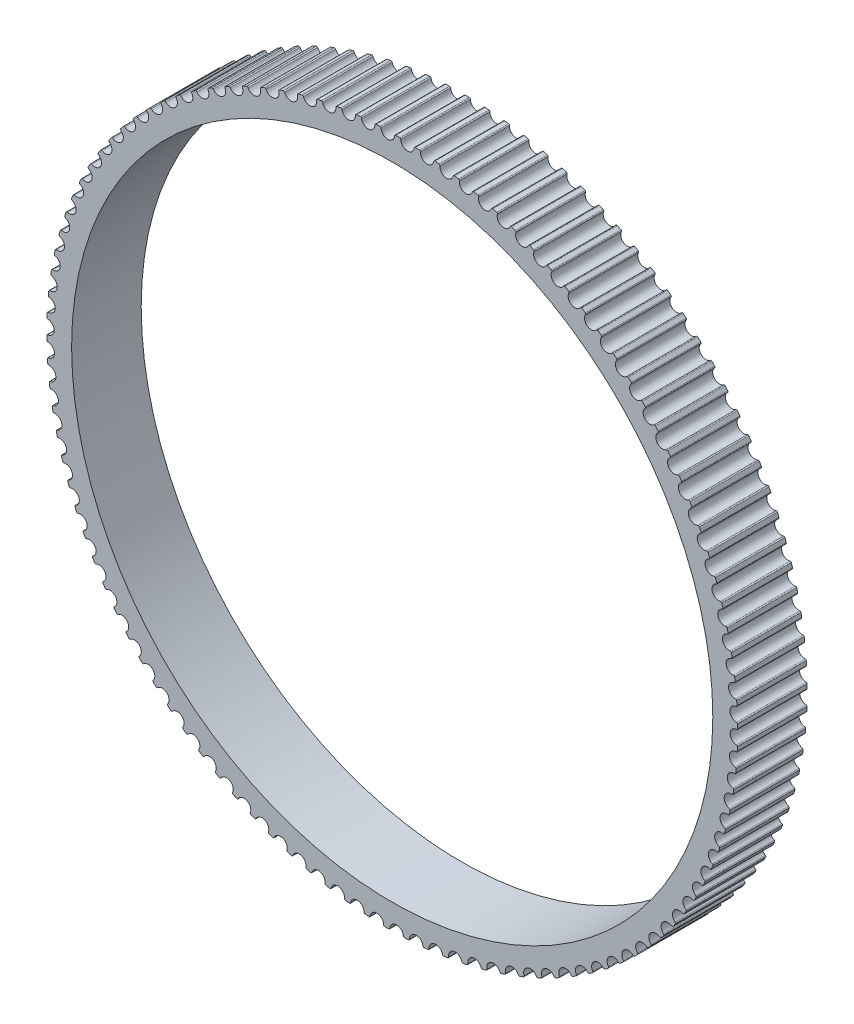
SolidWorks part; units mm, degrees
ref_plane "Front Plane" through (0, 0, 0) normal (0, 0, 1) x (1, 0, 0)
ref_plane "Top Plane" through (0, 0, 0) normal (0, 1, 0) x (1, 0, 0)
ref_plane "Right Plane" through (0, 0, 0) normal (1, 0, 0) x (0, 0, -1)
sketch "Sketch2" plane through (0, 0, 0) normal (0, 0, 1) x (1, 0, 0)
  circle A0 centre (0, 0) radius 35.03 construction
  arc A1 (-3.2113, 34.6013) -> (-3.0921, 34.5062) centre (-3.2012, 34.4918) cw
  arc A2 (-3.0921, 34.5062) -> (-1.738, 34.6009) centre (-2.418, 34.5956) ccw
  arc A3 (-1.738, 34.6009) -> (-1.6332, 34.7116) centre (-1.628, 34.6017) cw
  arc A4 (-1.6332, 34.7116) -> (-1.2307, 34.7282) centre (0, 0) cw
  circle A5 centre (0, 0) radius 34.75 construction
  circle A6 centre (0, 0) radius 34 construction
  arc A7 (0.3511, 34.7482) -> (0.7538, 34.7418) centre (0, 0) cw
  arc A8 (0.2401, 34.6437) -> (0.3511, 34.7482) centre (0.35, 34.6382) cw
  arc A9 (-1.1172, 34.6265) -> (0.2401, 34.6437) centre (-0.4391, 34.6772) ccw
  arc A10 (-1.2307, 34.7282) -> (-1.1172, 34.6265) centre (-1.2269, 34.6183) cw
  arc A11 (2.3343, 34.6715) -> (2.736, 34.6421) centre (0, 0) cw
  arc A12 (2.2175, 34.5735) -> (2.3343, 34.6715) centre (2.3269, 34.5618) cw
  arc A13 (0.8614, 34.6338) -> (2.2175, 34.5735) centre (1.5413, 34.6457) ccw
  arc A14 (0.7538, 34.7418) -> (0.8614, 34.6338) centre (0.7515, 34.6318) cw
  arc A15 (4.3098, 34.4817) -> (4.7092, 34.4294) centre (0, 0) cw
  arc A16 (4.1876, 34.3905) -> (4.3098, 34.4817) centre (4.2962, 34.3726) cw
  arc A17 (2.8372, 34.5281) -> (4.1876, 34.3905) centre (3.5167, 34.5012) ccw
  arc A18 (2.736, 34.6421) -> (2.8372, 34.5281) centre (2.7273, 34.5325) cw
  arc A19 (6.2713, 34.1794) -> (6.6671, 34.1044) centre (0, 0) cw
  arc A20 (6.1441, 34.0953) -> (6.2713, 34.1794) centre (6.2514, 34.0712) cw
  arc A21 (4.8038, 34.3098) -> (6.1441, 34.0953) centre (5.4806, 34.2442) ccw
  arc A22 (4.7092, 34.4294) -> (4.8038, 34.3098) centre (4.6943, 34.3204) cw
  arc A23 (8.2123, 33.7657) -> (8.6032, 33.6682) centre (0, 0) cw
  arc A24 (8.0806, 33.689) -> (8.2123, 33.7657) centre (8.1863, 33.6588) cw
  arc A25 (6.7547, 33.9796) -> (8.0806, 33.689) centre (7.4266, 33.8755) ccw
  arc A26 (6.6671, 34.1044) -> (6.7547, 33.9796) centre (6.646, 33.9965) cw
  arc A27 (10.1266, 33.2418) -> (10.5112, 33.1222) centre (0, 0) cw
  arc A28 (9.9906, 33.1727) -> (10.1266, 33.2418) centre (10.0945, 33.1365) cw
  arc A29 (8.6835, 33.5386) -> (9.9906, 33.1727) centre (9.3484, 33.3962) ccw
  arc A30 (8.6032, 33.6682) -> (8.6835, 33.5386) centre (8.5759, 33.5616) cw
  arc A31 (12.0078, 32.6094) -> (12.385, 32.4681) centre (0, 0) cw
  arc A32 (11.8681, 32.5482) -> (12.0078, 32.6094) centre (11.9698, 32.5062) cw
  arc A33 (10.584, 32.9882) -> (11.8681, 32.5482) centre (11.2397, 32.8081) ccw
  arc A34 (10.5112, 33.1222) -> (10.584, 32.9882) centre (10.4779, 33.0173) cw
  arc A35 (13.8498, 31.8707) -> (14.2183, 31.7081) centre (0, 0) cw
  arc A36 (13.7069, 31.8176) -> (13.8498, 31.8707) centre (13.806, 31.7699) cw
  arc A37 (12.45, 32.3301) -> (13.7069, 31.8176) centre (13.0944, 32.1129) ccw
  arc A38 (12.385, 32.4681) -> (12.45, 32.3301) centre (12.3458, 32.3653) cw
  arc A39 (15.6467, 31.0281) -> (16.0053, 30.8446) centre (0, 0) cw
  arc A40 (15.501, 30.9832) -> (15.6467, 31.0281) centre (15.5972, 30.9299) cw
  arc A41 (14.2754, 31.5667) -> (15.501, 30.9832) centre (14.9063, 31.313) ccw
  arc A42 (14.2183, 31.7081) -> (14.2754, 31.5667) centre (14.1733, 31.6077) cw
  arc A43 (17.3926, 30.0842) -> (17.7401, 29.8806) centre (0, 0) cw
  arc A44 (17.2445, 30.0478) -> (17.3926, 30.0842) centre (17.3375, 29.989) cw
  arc A45 (16.0542, 30.7002) -> (17.2445, 30.0478) centre (16.6696, 30.411) ccw
  arc A46 (16.0053, 30.8446) -> (16.0542, 30.7002) centre (15.9547, 30.747) cw
  arc A47 (19.0817, 29.0423) -> (19.417, 28.8191) centre (0, 0) cw
  arc A48 (18.9318, 29.0143) -> (19.0817, 29.0423) centre (19.0213, 28.9503) cw
  arc A49 (17.7807, 29.7336) -> (18.9318, 29.0143) centre (18.3786, 29.4097) ccw
  arc A50 (17.7401, 29.8806) -> (17.7807, 29.7336) centre (17.684, 29.786) cw
  arc A51 (20.7085, 27.9055) -> (21.0306, 27.6636) centre (0, 0) cw
  arc A52 (20.5573, 27.8862) -> (20.7085, 27.9055) centre (20.643, 27.8172) cw
  arc A53 (19.4491, 28.6701) -> (20.5573, 27.8862) centre (20.0276, 28.3125) ccw
  arc A54 (19.417, 28.8191) -> (19.4491, 28.6701) centre (19.3556, 28.7279) cw
  arc A55 (22.2679, 26.6778) -> (22.5756, 26.4179) centre (0, 0) cw
  arc A56 (22.1158, 26.6671) -> (22.2679, 26.6778) centre (22.1974, 26.5934) cw
  arc A57 (21.0542, 27.513) -> (22.1158, 26.6671) centre (21.6112, 27.123) ccw
  arc A58 (21.0306, 27.6636) -> (21.0542, 27.513) centre (20.964, 27.5761) cw
  arc A59 (23.7545, 25.363) -> (24.0469, 25.086) centre (0, 0) cw
  arc A60 (23.6021, 25.361) -> (23.7545, 25.363) centre (23.6793, 25.2828) cw
  arc A61 (22.5905, 26.2661) -> (23.6021, 25.361) centre (23.1244, 25.845) ccw
  arc A62 (22.5756, 26.4179) -> (22.5905, 26.2661) centre (22.5041, 26.3343) cw
  arc A63 (25.1637, 23.9656) -> (25.4399, 23.6723) centre (0, 0) cw
  arc A64 (25.0114, 23.9723) -> (25.1637, 23.9656) centre (25.0841, 23.8897) cw
  arc A65 (24.0532, 24.9336) -> (25.0114, 23.9723) centre (24.5621, 24.4827) ccw
  arc A66 (24.0469, 25.086) -> (24.0532, 24.9336) centre (23.9708, 25.0066) cw
  arc A67 (26.4909, 22.4899) -> (26.7498, 22.1813) centre (0, 0) cw
  arc A68 (26.3392, 22.5053) -> (26.4909, 22.4899) centre (26.407, 22.4187) cw
  arc A69 (25.4374, 23.5198) -> (26.3392, 22.5053) centre (25.9198, 23.0406) ccw
  arc A70 (25.4399, 23.6723) -> (25.4374, 23.5198) centre (25.3593, 23.5973) cw
  arc A71 (27.7316, 20.9409) -> (27.9725, 20.618) centre (0, 0) cw
  arc A72 (27.581, 20.9649) -> (27.7316, 20.9409) centre (27.6438, 20.8746) cw
  arc A73 (26.7386, 22.0293) -> (27.581, 20.9649) centre (27.1929, 21.5233) ccw
  arc A74 (26.7498, 22.1813) -> (26.7386, 22.0293) centre (26.6651, 22.1111) cw
  arc A75 (28.8819, 19.3236) -> (29.1039, 18.9875) centre (0, 0) cw
  arc A76 (28.7329, 19.3562) -> (28.8819, 19.3236) centre (28.7904, 19.2624) cw
  arc A77 (27.9526, 20.4669) -> (28.7329, 19.3562) centre (28.3772, 19.9358) ccw
  arc A78 (27.9725, 20.618) -> (27.9526, 20.4669) centre (27.8839, 20.5528) cw
  arc A79 (29.9379, 17.6432) -> (30.1404, 17.295) centre (0, 0) cw
  arc A80 (29.7911, 17.6843) -> (29.9379, 17.6432) centre (29.8431, 17.5874) cw
  arc A81 (29.0755, 18.8377) -> (29.7911, 17.6843) centre (29.4691, 18.2832) ccw
  arc A82 (29.1039, 18.9875) -> (29.0755, 18.8377) centre (29.0118, 18.9274) cw
  arc A83 (30.8963, 15.9053) -> (31.0786, 15.5461) centre (0, 0) cw
  arc A84 (30.752, 15.9547) -> (30.8963, 15.9053) centre (30.7985, 15.855) cw
  arc A85 (30.1035, 17.1471) -> (30.752, 15.9547) centre (30.4648, 16.571) ccw
  arc A86 (30.1404, 17.295) -> (30.1035, 17.1471) centre (30.045, 17.2403) cw
  arc A87 (31.7539, 14.1156) -> (31.9154, 13.7465) centre (0, 0) cw
  arc A88 (31.6127, 14.1731) -> (31.7539, 14.1156) centre (31.6534, 14.0709) cw
  arc A89 (31.0333, 15.4006) -> (31.6127, 14.1731) centre (31.3611, 14.8048) ccw
  arc A90 (31.0786, 15.5461) -> (31.0333, 15.4006) centre (30.9802, 15.4969) cw
  arc A91 (32.508, 12.2798) -> (32.6482, 11.9021) centre (0, 0) cw
  arc A92 (32.3703, 12.3452) -> (32.508, 12.2798) centre (32.4051, 12.2409) cw
  arc A93 (31.8619, 13.6038) -> (32.3703, 12.3452) centre (32.1552, 12.9903) ccw
  arc A94 (31.9154, 13.7465) -> (31.8619, 13.6038) centre (31.8144, 13.703) cw
  arc A95 (33.156, 10.4039) -> (33.2744, 10.0189) centre (0, 0) cw
  arc A96 (33.0223, 10.4771) -> (33.156, 10.4039) centre (33.0511, 10.371) cw
  arc A97 (32.5865, 11.7627) -> (33.0223, 10.4771) centre (32.8443, 11.1334) ccw
  arc A98 (32.6482, 11.9021) -> (32.5865, 11.7627) centre (32.5448, 11.8644) cw
  arc A99 (33.6959, 8.4941) -> (33.7921, 8.1029) centre (0, 0) cw
  arc A100 (33.5665, 8.5748) -> (33.6959, 8.4941) centre (33.5892, 8.4672) cw
  arc A101 (33.2049, 9.8831) -> (33.5665, 8.5748) centre (33.4263, 9.2402) ccw
  arc A102 (33.2744, 10.0189) -> (33.2049, 9.8831) centre (33.1691, 9.9871) cw
  arc A103 (34.1259, 6.5566) -> (34.1996, 6.1606) centre (0, 0) cw
  arc A104 (34.0013, 6.6446) -> (34.1259, 6.5566) centre (34.0178, 6.5358) cw
  arc A105 (33.7149, 7.9714) -> (34.0013, 6.6446) centre (33.8993, 7.3169) ccw
  arc A106 (33.7921, 8.1029) -> (33.7149, 7.9714) centre (33.6851, 8.0773) cw
  arc A107 (34.4445, 4.5977) -> (34.4955, 4.1981) centre (0, 0) cw
  arc A108 (34.3252, 4.6926) -> (34.4445, 4.5977) centre (34.3355, 4.5831) cw
  arc A109 (34.115, 6.0337) -> (34.3252, 4.6926) centre (34.2618, 5.3697) ccw
  arc A110 (34.1996, 6.1606) -> (34.115, 6.0337) centre (34.0913, 6.1411) cw
  arc A111 (34.6508, 2.6238) -> (34.6789, 2.2219) centre (0, 0) cw
  arc A112 (34.5371, 2.7254) -> (34.6508, 2.6238) centre (34.5411, 2.6155) cw
  arc A113 (34.4039, 4.0762) -> (34.5371, 2.7254) centre (34.5124, 3.4049) ccw
  arc A114 (34.4955, 4.1981) -> (34.4039, 4.0762) centre (34.3863, 4.1848) cw
  arc A115 (34.7441, 0.6413) -> (34.7492, 0.2385) centre (0, 0) cw
  arc A116 (34.6364, 0.7493) -> (34.7441, 0.6413) centre (34.6341, 0.6393) cw
  arc A117 (34.5805, 2.1055) -> (34.6364, 0.7493) centre (34.6505, 1.4291) ccw
  arc A118 (34.6789, 2.2219) -> (34.5805, 2.1055) centre (34.5691, 2.2149) cw
  arc A119 (34.724, -1.3432) -> (34.7061, -1.7456) centre (0, 0) cw
  arc A120 (34.6227, -1.2293) -> (34.724, -1.3432) centre (34.6141, -1.339) cw
  arc A121 (34.6443, 0.1279) -> (34.6227, -1.2293) centre (34.6756, -0.5514) ccw
  arc A122 (34.7492, 0.2385) -> (34.6443, 0.1279) centre (34.6392, 0.2378) cw
  arc A123 (34.5907, -3.3234) -> (34.5499, -3.7241) centre (0, 0) cw
  arc A124 (34.496, -3.2039) -> (34.5907, -3.3234) centre (34.4812, -3.3129) cw
  arc A125 (34.5951, -1.8501) -> (34.496, -3.2039) centre (34.5876, -2.5301) ccw
  arc A126 (34.7061, -1.7456) -> (34.5951, -1.8501) centre (34.5963, -1.7401) cw
  arc A127 (34.3446, -5.2927) -> (34.2809, -5.6905) centre (0, 0) cw
  arc A128 (34.2569, -5.168) -> (34.3446, -5.2927) centre (34.2359, -5.276) cw
  arc A129 (34.433, -3.8221) -> (34.2569, -5.168) centre (34.3867, -4.5005) ccw
  arc A130 (34.5499, -3.7241) -> (34.433, -3.8221) centre (34.4405, -3.7123) cw
  arc A131 (33.9864, -7.2448) -> (33.9001, -7.6382) centre (0, 0) cw
  arc A132 (33.906, -7.1152) -> (33.9864, -7.2448) centre (33.8788, -7.2218) cw
  arc A133 (34.1587, -5.7816) -> (33.906, -7.1152) centre (34.0737, -6.4563) ccw
  arc A134 (34.2809, -5.6905) -> (34.1587, -5.7816) centre (34.1724, -5.6724) cw
  arc A135 (33.5174, -9.1732) -> (33.4088, -9.5611) centre (0, 0) cw
  arc A136 (33.4445, -9.0393) -> (33.5174, -9.1732) centre (33.4113, -9.1442) cw
  arc A137 (33.7729, -7.7222) -> (33.4445, -9.0393) centre (33.6496, -8.391) ccw
  arc A138 (33.9001, -7.6382) -> (33.7729, -7.7222) centre (33.7928, -7.6141) cw
  arc A139 (32.939, -11.0717) -> (32.8085, -11.4528) centre (0, 0) cw
  arc A140 (32.8739, -10.9338) -> (32.939, -11.0717) centre (32.8348, -11.0367) cw
  arc A141 (33.277, -9.6377) -> (32.8739, -10.9338) centre (33.1157, -10.2983) ccw
  arc A142 (33.4088, -9.5611) -> (33.277, -9.6377) centre (33.303, -9.5308) cw
  arc A143 (32.2532, -12.9341) -> (32.1012, -13.3071) centre (0, 0) cw
  arc A144 (32.1961, -12.7927) -> (32.2532, -12.9341) centre (32.1511, -12.8932) cw
  arc A145 (32.6725, -11.5217) -> (32.1961, -12.7927) centre (32.4737, -12.172) ccw
  arc A146 (32.8085, -11.4528) -> (32.6725, -11.5217) centre (32.7046, -11.4165) cw
  arc A147 (31.4622, -14.7543) -> (31.2891, -15.118) centre (0, 0) cw
  arc A148 (31.4132, -14.6099) -> (31.4622, -14.7543) centre (31.3627, -14.7076) cw
  arc A149 (31.9614, -13.3682) -> (31.4132, -14.6099) centre (31.7259, -14.0061) ccw
  arc A150 (32.1012, -13.3071) -> (31.9614, -13.3682) centre (31.9995, -13.265) cw
  arc A151 (30.5686, -16.5264) -> (30.375, -16.8796) centre (0, 0) cw
  arc A152 (30.5279, -16.3794) -> (30.5686, -16.5264) centre (30.4719, -16.4741) cw
  arc A153 (31.1461, -15.171) -> (30.5279, -16.3794) centre (30.8746, -15.7944) ccw
  arc A154 (31.2891, -15.118) -> (31.1461, -15.171) centre (31.1901, -15.0701) cw
  arc A155 (29.5753, -18.2446) -> (29.3618, -18.5861) centre (0, 0) cw
  arc A156 (29.5431, -18.0955) -> (29.5753, -18.2446) centre (29.4817, -18.1868) cw
  arc A157 (30.2292, -16.9243) -> (29.5431, -18.0955) centre (29.9225, -17.5312) ccw
  arc A158 (30.375, -16.8796) -> (30.2292, -16.9243) centre (30.2789, -16.8262) cw
  arc A159 (28.4855, -19.9032) -> (28.2529, -20.2321) centre (0, 0) cw
  arc A160 (28.4618, -19.7526) -> (28.4855, -19.9032) centre (28.3953, -19.8402) cw
  arc A161 (29.2138, -18.6225) -> (28.4618, -19.7526) centre (28.8729, -19.2109) ccw
  arc A162 (29.3618, -18.5861) -> (29.2138, -18.6225) centre (29.2689, -18.5273) cw
  arc A163 (27.3028, -21.497) -> (27.0518, -21.812) centre (0, 0) cw
  arc A164 (27.2878, -21.3452) -> (27.3028, -21.497) centre (27.2164, -21.4289) cw
  arc A165 (28.103, -20.2599) -> (27.2878, -21.3452) centre (27.7291, -20.8279) ccw
  arc A166 (28.2529, -20.2321) -> (28.103, -20.2599) centre (28.1635, -20.168) cw
  arc A167 (26.031, -23.0206) -> (25.7625, -23.3208) centre (0, 0) cw
  arc A168 (26.0247, -22.8682) -> (26.031, -23.0206) centre (25.9486, -22.9477) cw
  arc A169 (26.9005, -21.8312) -> (26.0247, -22.8682) centre (26.4948, -22.3769) ccw
  arc A170 (27.0518, -21.812) -> (26.9005, -21.8312) centre (26.9662, -21.743) cw
  arc A171 (24.6744, -24.4691) -> (24.3891, -24.7535) centre (0, 0) cw
  arc A172 (24.6767, -24.3167) -> (24.6744, -24.4691) centre (24.5963, -24.3917) cw
  arc A173 (25.6103, -23.3313) -> (24.6767, -24.3167) centre (25.1741, -23.853) ccw
  arc A174 (25.7625, -23.3208) -> (25.6103, -23.3313) centre (25.6809, -23.247) cw
  arc A175 (23.2372, -25.8378) -> (22.9362, -26.1055) centre (0, 0) cw
  arc A176 (23.2483, -25.6858) -> (23.2372, -25.8378) centre (23.1637, -25.7561) cw
  arc A177 (24.2366, -24.7554) -> (23.2483, -25.6858) centre (23.7713, -25.2513) ccw
  arc A178 (24.3891, -24.7535) -> (24.2366, -24.7554) centre (24.3119, -24.6751) cw
  arc A179 (21.7243, -27.1223) -> (21.4084, -27.3723) centre (0, 0) cw
  arc A180 (21.744, -26.9711) -> (21.7243, -27.1223) centre (21.6555, -27.0364) cw
  arc A181 (22.7838, -26.0986) -> (21.744, -26.9711) centre (22.291, -26.5672) ccw
  arc A182 (22.9362, -26.1055) -> (22.7838, -26.0986) centre (22.8636, -26.0228) cw
  arc A183 (20.1405, -28.3183) -> (19.8109, -28.5498) centre (0, 0) cw
  arc A184 (20.1688, -28.1684) -> (20.1405, -28.3183) centre (20.0767, -28.2286) cw
  arc A185 (21.2567, -27.3568) -> (20.1688, -28.1684) centre (20.738, -27.7964) ccw
  arc A186 (21.4084, -27.3723) -> (21.2567, -27.3568) centre (21.3407, -27.2856) cw
  arc A187 (18.491, -29.4219) -> (18.1487, -29.6342) centre (0, 0) cw
  arc A188 (18.5278, -29.2739) -> (18.491, -29.4219) centre (18.4324, -29.3287) cw
  arc A189 (19.6603, -28.5257) -> (18.5278, -29.2739) centre (19.1173, -28.935) ccw
  arc A190 (19.8109, -28.5498) -> (19.6603, -28.5257) centre (19.7481, -28.4595) cw
  arc A191 (16.7811, -30.4295) -> (16.4273, -30.622) centre (0, 0) cw
  arc A192 (16.8263, -30.2839) -> (16.7811, -30.4295) centre (16.728, -30.3332) cw
  arc A193 (17.9997, -29.6015) -> (16.8263, -30.2839) centre (17.4342, -29.9792) ccw
  arc A194 (18.1487, -29.6342) -> (17.9997, -29.6015) centre (18.0912, -29.5404) cw
  arc A195 (15.0166, -31.3379) -> (14.6523, -31.5099) centre (0, 0) cw
  arc A196 (15.07, -31.1951) -> (15.0166, -31.3379) centre (14.969, -31.2387) cw
  arc A197 (16.2805, -30.5808) -> (15.07, -31.1951) centre (15.6943, -30.9256) ccw
  arc A198 (16.4273, -30.622) -> (16.2805, -30.5808) centre (16.3753, -30.5251) cw
  arc A199 (13.203, -32.1441) -> (12.8296, -32.295) centre (0, 0) cw
  arc A200 (13.2646, -32.0046) -> (13.203, -32.1441) centre (13.1613, -32.0423) cw
  arc A201 (14.5081, -31.4604) -> (13.2646, -32.0046) centre (13.9032, -31.7711) ccw
  arc A202 (14.6523, -31.5099) -> (14.5081, -31.4604) centre (14.6059, -31.4101) cw
  arc A203 (11.3464, -32.8454) -> (10.965, -32.9747) centre (0, 0) cw
  arc A204 (11.4158, -32.7096) -> (11.3464, -32.8454) centre (11.3105, -32.7414) cw
  arc A205 (12.6884, -32.2373) -> (11.4158, -32.7096) centre (12.0668, -32.513) ccw
  arc A206 (12.8296, -32.295) -> (12.6884, -32.2373) centre (12.789, -32.1927) cw
  arc A207 (9.4528, -33.4396) -> (9.0646, -33.5469) centre (0, 0) cw
  arc A208 (9.5299, -33.308) -> (9.4528, -33.4396) centre (9.4229, -33.3337) cw
  arc A209 (10.8273, -32.9091) -> (9.5299, -33.308) centre (10.191, -33.1489) ccw
  arc A210 (10.965, -32.9747) -> (10.8273, -32.9091) centre (10.9302, -32.8703) cw
  arc A211 (7.5284, -33.9247) -> (7.1347, -34.0097) centre (0, 0) cw
  arc A212 (7.6128, -33.7977) -> (7.5284, -33.9247) centre (7.5046, -33.8173) cw
  arc A213 (8.9309, -33.4736) -> (7.6128, -33.7977) centre (8.2819, -33.6766) ccw
  arc A214 (9.0646, -33.5469) -> (8.9309, -33.4736) centre (9.0359, -33.4407) cw
  arc A215 (5.5794, -34.2992) -> (5.1814, -34.3615) centre (0, 0) cw
  arc A216 (5.6709, -34.1772) -> (5.5794, -34.2992) centre (5.5617, -34.1906) cw
  arc A217 (7.0054, -33.9288) -> (5.6709, -34.1772) centre (6.3459, -34.0945) ccw
  arc A218 (7.1347, -34.0097) -> (7.0054, -33.9288) centre (7.1121, -33.902) cw
  arc A219 (3.6122, -34.5617) -> (3.2113, -34.6013) centre (0, 0) cw
  arc A220 (3.7105, -34.4452) -> (3.6122, -34.5617) centre (3.6008, -34.4523) cw
  arc A221 (5.057, -34.2734) -> (3.7105, -34.4452) centre (4.3891, -34.4011) ccw
  arc A222 (5.1814, -34.3615) -> (5.057, -34.2734) centre (5.165, -34.2528) cw
  arc A223 (1.6332, -34.7116) -> (1.2307, -34.7282) centre (0, 0) cw
  arc A224 (1.738, -34.6009) -> (1.6332, -34.7116) centre (1.628, -34.6017) cw
  arc A225 (3.0921, -34.5062) -> (1.738, -34.6009) centre (2.418, -34.5956) ccw
  arc A226 (3.2113, -34.6013) -> (3.0921, -34.5062) centre (3.2012, -34.4918) cw
  arc A227 (-0.3511, -34.7482) -> (-0.7538, -34.7418) centre (0, 0) cw
  arc A228 (-0.2401, -34.6437) -> (-0.3511, -34.7482) centre (-0.35, -34.6382) cw
  arc A229 (1.1172, -34.6265) -> (-0.2401, -34.6437) centre (0.4391, -34.6772) ccw
  arc A230 (1.2307, -34.7282) -> (1.1172, -34.6265) centre (1.2269, -34.6183) cw
  arc A231 (-2.3343, -34.6715) -> (-2.736, -34.6421) centre (0, 0) cw
  arc A232 (-2.2175, -34.5735) -> (-2.3343, -34.6715) centre (-2.3269, -34.5618) cw
  arc A233 (-0.8614, -34.6338) -> (-2.2175, -34.5735) centre (-1.5413, -34.6457) ccw
  arc A234 (-0.7538, -34.7418) -> (-0.8614, -34.6338) centre (-0.7515, -34.6318) cw
  arc A235 (-4.3098, -34.4817) -> (-4.7092, -34.4294) centre (0, 0) cw
  arc A236 (-4.1876, -34.3905) -> (-4.3098, -34.4817) centre (-4.2962, -34.3726) cw
  arc A237 (-2.8372, -34.5281) -> (-4.1876, -34.3905) centre (-3.5167, -34.5012) ccw
  arc A238 (-2.736, -34.6421) -> (-2.8372, -34.5281) centre (-2.7273, -34.5325) cw
  arc A239 (-6.2713, -34.1794) -> (-6.6671, -34.1044) centre (0, 0) cw
  arc A240 (-6.1441, -34.0953) -> (-6.2713, -34.1794) centre (-6.2514, -34.0712) cw
  arc A241 (-4.8038, -34.3098) -> (-6.1441, -34.0953) centre (-5.4806, -34.2442) ccw
  arc A242 (-4.7092, -34.4294) -> (-4.8038, -34.3098) centre (-4.6943, -34.3204) cw
  arc A243 (-8.2123, -33.7657) -> (-8.6032, -33.6682) centre (0, 0) cw
  arc A244 (-8.0806, -33.689) -> (-8.2123, -33.7657) centre (-8.1863, -33.6588) cw
  arc A245 (-6.7547, -33.9796) -> (-8.0806, -33.689) centre (-7.4266, -33.8755) ccw
  arc A246 (-6.6671, -34.1044) -> (-6.7547, -33.9796) centre (-6.646, -33.9965) cw
  arc A247 (-10.1266, -33.2418) -> (-10.5112, -33.1222) centre (0, 0) cw
  arc A248 (-9.9906, -33.1727) -> (-10.1266, -33.2418) centre (-10.0945, -33.1365) cw
  arc A249 (-8.6835, -33.5386) -> (-9.9906, -33.1727) centre (-9.3484, -33.3962) ccw
  arc A250 (-8.6032, -33.6682) -> (-8.6835, -33.5386) centre (-8.5759, -33.5616) cw
  arc A251 (-12.0078, -32.6094) -> (-12.385, -32.4681) centre (0, 0) cw
  arc A252 (-11.8681, -32.5482) -> (-12.0078, -32.6094) centre (-11.9698, -32.5062) cw
  arc A253 (-10.584, -32.9882) -> (-11.8681, -32.5482) centre (-11.2397, -32.8081) ccw
  arc A254 (-10.5112, -33.1222) -> (-10.584, -32.9882) centre (-10.4779, -33.0173) cw
  arc A255 (-13.8498, -31.8707) -> (-14.2183, -31.7081) centre (0, 0) cw
  arc A256 (-13.7069, -31.8176) -> (-13.8498, -31.8707) centre (-13.806, -31.7699) cw
  arc A257 (-12.45, -32.3301) -> (-13.7069, -31.8176) centre (-13.0944, -32.1129) ccw
  arc A258 (-12.385, -32.4681) -> (-12.45, -32.3301) centre (-12.3458, -32.3653) cw
  arc A259 (-15.6467, -31.0281) -> (-16.0053, -30.8446) centre (0, 0) cw
  arc A260 (-15.501, -30.9832) -> (-15.6467, -31.0281) centre (-15.5972, -30.9299) cw
  arc A261 (-14.2754, -31.5667) -> (-15.501, -30.9832) centre (-14.9063, -31.313) ccw
  arc A262 (-14.2183, -31.7081) -> (-14.2754, -31.5667) centre (-14.1733, -31.6077) cw
  arc A263 (-17.3926, -30.0842) -> (-17.7401, -29.8806) centre (0, 0) cw
  arc A264 (-17.2445, -30.0478) -> (-17.3926, -30.0842) centre (-17.3375, -29.989) cw
  arc A265 (-16.0542, -30.7002) -> (-17.2445, -30.0478) centre (-16.6696, -30.411) ccw
  arc A266 (-16.0053, -30.8446) -> (-16.0542, -30.7002) centre (-15.9547, -30.747) cw
  arc A267 (-19.0817, -29.0423) -> (-19.417, -28.8191) centre (0, 0) cw
  arc A268 (-18.9318, -29.0143) -> (-19.0817, -29.0423) centre (-19.0213, -28.9503) cw
  arc A269 (-17.7807, -29.7336) -> (-18.9318, -29.0143) centre (-18.3786, -29.4097) ccw
  arc A270 (-17.7401, -29.8806) -> (-17.7807, -29.7336) centre (-17.684, -29.786) cw
  arc A271 (-20.7085, -27.9055) -> (-21.0306, -27.6636) centre (0, 0) cw
  arc A272 (-20.5573, -27.8862) -> (-20.7085, -27.9055) centre (-20.643, -27.8172) cw
  arc A273 (-19.4491, -28.6701) -> (-20.5573, -27.8862) centre (-20.0276, -28.3125) ccw
  arc A274 (-19.417, -28.8191) -> (-19.4491, -28.6701) centre (-19.3556, -28.7279) cw
  arc A275 (-22.2679, -26.6778) -> (-22.5756, -26.4179) centre (0, 0) cw
  arc A276 (-22.1158, -26.6671) -> (-22.2679, -26.6778) centre (-22.1974, -26.5934) cw
  arc A277 (-21.0542, -27.513) -> (-22.1158, -26.6671) centre (-21.6112, -27.123) ccw
  arc A278 (-21.0306, -27.6636) -> (-21.0542, -27.513) centre (-20.964, -27.5761) cw
  arc A279 (-23.7545, -25.363) -> (-24.0469, -25.086) centre (0, 0) cw
  arc A280 (-23.6021, -25.361) -> (-23.7545, -25.363) centre (-23.6793, -25.2828) cw
  arc A281 (-22.5905, -26.2661) -> (-23.6021, -25.361) centre (-23.1244, -25.845) ccw
  arc A282 (-22.5756, -26.4179) -> (-22.5905, -26.2661) centre (-22.5041, -26.3343) cw
  arc A283 (-25.1637, -23.9656) -> (-25.4399, -23.6723) centre (0, 0) cw
  arc A284 (-25.0114, -23.9723) -> (-25.1637, -23.9656) centre (-25.0841, -23.8897) cw
  arc A285 (-24.0532, -24.9336) -> (-25.0114, -23.9723) centre (-24.5621, -24.4827) ccw
  arc A286 (-24.0469, -25.086) -> (-24.0532, -24.9336) centre (-23.9708, -25.0066) cw
  arc A287 (-26.4909, -22.4899) -> (-26.7498, -22.1813) centre (0, 0) cw
  arc A288 (-26.3392, -22.5053) -> (-26.4909, -22.4899) centre (-26.407, -22.4187) cw
  arc A289 (-25.4374, -23.5198) -> (-26.3392, -22.5053) centre (-25.9198, -23.0406) ccw
  arc A290 (-25.4399, -23.6723) -> (-25.4374, -23.5198) centre (-25.3593, -23.5973) cw
  arc A291 (-27.7316, -20.9409) -> (-27.9725, -20.618) centre (0, 0) cw
  arc A292 (-27.581, -20.9649) -> (-27.7316, -20.9409) centre (-27.6438, -20.8746) cw
  arc A293 (-26.7386, -22.0293) -> (-27.581, -20.9649) centre (-27.1929, -21.5233) ccw
  arc A294 (-26.7498, -22.1813) -> (-26.7386, -22.0293) centre (-26.6651, -22.1111) cw
  arc A295 (-28.8819, -19.3236) -> (-29.1039, -18.9875) centre (0, 0) cw
  arc A296 (-28.7329, -19.3562) -> (-28.8819, -19.3236) centre (-28.7904, -19.2624) cw
  arc A297 (-27.9526, -20.4669) -> (-28.7329, -19.3562) centre (-28.3772, -19.9358) ccw
  arc A298 (-27.9725, -20.618) -> (-27.9526, -20.4669) centre (-27.8839, -20.5528) cw
  arc A299 (-29.9379, -17.6432) -> (-30.1404, -17.295) centre (0, 0) cw
  arc A300 (-29.7911, -17.6843) -> (-29.9379, -17.6432) centre (-29.8431, -17.5874) cw
  arc A301 (-29.0755, -18.8377) -> (-29.7911, -17.6843) centre (-29.4691, -18.2832) ccw
  arc A302 (-29.1039, -18.9875) -> (-29.0755, -18.8377) centre (-29.0118, -18.9274) cw
  arc A303 (-30.8963, -15.9053) -> (-31.0786, -15.5461) centre (0, 0) cw
  arc A304 (-30.752, -15.9547) -> (-30.8963, -15.9053) centre (-30.7985, -15.855) cw
  arc A305 (-30.1035, -17.1471) -> (-30.752, -15.9547) centre (-30.4648, -16.571) ccw
  arc A306 (-30.1404, -17.295) -> (-30.1035, -17.1471) centre (-30.045, -17.2403) cw
  arc A307 (-31.7539, -14.1156) -> (-31.9154, -13.7465) centre (0, 0) cw
  arc A308 (-31.6127, -14.1731) -> (-31.7539, -14.1156) centre (-31.6534, -14.0709) cw
  arc A309 (-31.0333, -15.4006) -> (-31.6127, -14.1731) centre (-31.3611, -14.8048) ccw
  arc A310 (-31.0786, -15.5461) -> (-31.0333, -15.4006) centre (-30.9802, -15.4969) cw
  arc A311 (-32.508, -12.2798) -> (-32.6482, -11.9021) centre (0, 0) cw
  arc A312 (-32.3703, -12.3452) -> (-32.508, -12.2798) centre (-32.4051, -12.2409) cw
  arc A313 (-31.8619, -13.6038) -> (-32.3703, -12.3452) centre (-32.1552, -12.9903) ccw
  arc A314 (-31.9154, -13.7465) -> (-31.8619, -13.6038) centre (-31.8144, -13.703) cw
  arc A315 (-33.156, -10.4039) -> (-33.2744, -10.0189) centre (0, 0) cw
  arc A316 (-33.0223, -10.4771) -> (-33.156, -10.4039) centre (-33.0511, -10.371) cw
  arc A317 (-32.5865, -11.7627) -> (-33.0223, -10.4771) centre (-32.8443, -11.1334) ccw
  arc A318 (-32.6482, -11.9021) -> (-32.5865, -11.7627) centre (-32.5448, -11.8644) cw
  arc A319 (-33.6959, -8.4941) -> (-33.7921, -8.1029) centre (0, 0) cw
  arc A320 (-33.5665, -8.5748) -> (-33.6959, -8.4941) centre (-33.5892, -8.4672) cw
  arc A321 (-33.2049, -9.8831) -> (-33.5665, -8.5748) centre (-33.4263, -9.2402) ccw
  arc A322 (-33.2744, -10.0189) -> (-33.2049, -9.8831) centre (-33.1691, -9.9871) cw
  arc A323 (-34.1259, -6.5566) -> (-34.1996, -6.1606) centre (0, 0) cw
  arc A324 (-34.0013, -6.6446) -> (-34.1259, -6.5566) centre (-34.0178, -6.5358) cw
  arc A325 (-33.7149, -7.9714) -> (-34.0013, -6.6446) centre (-33.8993, -7.3169) ccw
  arc A326 (-33.7921, -8.1029) -> (-33.7149, -7.9714) centre (-33.6851, -8.0773) cw
  arc A327 (-34.4445, -4.5977) -> (-34.4955, -4.1981) centre (0, 0) cw
  arc A328 (-34.3252, -4.6926) -> (-34.4445, -4.5977) centre (-34.3355, -4.5831) cw
  arc A329 (-34.115, -6.0337) -> (-34.3252, -4.6926) centre (-34.2618, -5.3697) ccw
  arc A330 (-34.1996, -6.1606) -> (-34.115, -6.0337) centre (-34.0913, -6.1411) cw
  arc A331 (-34.6508, -2.6238) -> (-34.6789, -2.2219) centre (0, 0) cw
  arc A332 (-34.5371, -2.7254) -> (-34.6508, -2.6238) centre (-34.5411, -2.6155) cw
  arc A333 (-34.4039, -4.0762) -> (-34.5371, -2.7254) centre (-34.5124, -3.4049) ccw
  arc A334 (-34.4955, -4.1981) -> (-34.4039, -4.0762) centre (-34.3863, -4.1848) cw
  arc A335 (-34.7441, -0.6413) -> (-34.7492, -0.2385) centre (0, 0) cw
  arc A336 (-34.6364, -0.7493) -> (-34.7441, -0.6413) centre (-34.6341, -0.6393) cw
  arc A337 (-34.5805, -2.1055) -> (-34.6364, -0.7493) centre (-34.6505, -1.4291) ccw
  arc A338 (-34.6789, -2.2219) -> (-34.5805, -2.1055) centre (-34.5691, -2.2149) cw
  arc A339 (-34.724, 1.3432) -> (-34.7061, 1.7456) centre (0, 0) cw
  arc A340 (-34.6227, 1.2293) -> (-34.724, 1.3432) centre (-34.6141, 1.339) cw
  arc A341 (-34.6443, -0.1279) -> (-34.6227, 1.2293) centre (-34.6756, 0.5514) ccw
  arc A342 (-34.7492, -0.2385) -> (-34.6443, -0.1279) centre (-34.6392, -0.2378) cw
  arc A343 (-34.5907, 3.3234) -> (-34.5499, 3.7241) centre (0, 0) cw
  arc A344 (-34.496, 3.2039) -> (-34.5907, 3.3234) centre (-34.4812, 3.3129) cw
  arc A345 (-34.5951, 1.8501) -> (-34.496, 3.2039) centre (-34.5876, 2.5301) ccw
  arc A346 (-34.7061, 1.7456) -> (-34.5951, 1.8501) centre (-34.5963, 1.7401) cw
  arc A347 (-34.3446, 5.2927) -> (-34.2809, 5.6905) centre (0, 0) cw
  arc A348 (-34.2569, 5.168) -> (-34.3446, 5.2927) centre (-34.2359, 5.276) cw
  arc A349 (-34.433, 3.8221) -> (-34.2569, 5.168) centre (-34.3867, 4.5005) ccw
  arc A350 (-34.5499, 3.7241) -> (-34.433, 3.8221) centre (-34.4405, 3.7123) cw
  arc A351 (-33.9864, 7.2448) -> (-33.9001, 7.6382) centre (0, 0) cw
  arc A352 (-33.906, 7.1152) -> (-33.9864, 7.2448) centre (-33.8788, 7.2218) cw
  arc A353 (-34.1587, 5.7816) -> (-33.906, 7.1152) centre (-34.0737, 6.4563) ccw
  arc A354 (-34.2809, 5.6905) -> (-34.1587, 5.7816) centre (-34.1724, 5.6724) cw
  arc A355 (-33.5174, 9.1732) -> (-33.4088, 9.5611) centre (0, 0) cw
  arc A356 (-33.4445, 9.0393) -> (-33.5174, 9.1732) centre (-33.4113, 9.1442) cw
  arc A357 (-33.7729, 7.7222) -> (-33.4445, 9.0393) centre (-33.6496, 8.391) ccw
  arc A358 (-33.9001, 7.6382) -> (-33.7729, 7.7222) centre (-33.7928, 7.6141) cw
  arc A359 (-32.939, 11.0717) -> (-32.8085, 11.4528) centre (0, 0) cw
  arc A360 (-32.8739, 10.9338) -> (-32.939, 11.0717) centre (-32.8348, 11.0367) cw
  arc A361 (-33.277, 9.6377) -> (-32.8739, 10.9338) centre (-33.1157, 10.2983) ccw
  arc A362 (-33.4088, 9.5611) -> (-33.277, 9.6377) centre (-33.303, 9.5308) cw
  arc A363 (-32.2532, 12.9341) -> (-32.1012, 13.3071) centre (0, 0) cw
  arc A364 (-32.1961, 12.7927) -> (-32.2532, 12.9341) centre (-32.1511, 12.8932) cw
  arc A365 (-32.6725, 11.5217) -> (-32.1961, 12.7927) centre (-32.4737, 12.172) ccw
  arc A366 (-32.8085, 11.4528) -> (-32.6725, 11.5217) centre (-32.7046, 11.4165) cw
  arc A367 (-31.4622, 14.7543) -> (-31.2891, 15.118) centre (0, 0) cw
  arc A368 (-31.4132, 14.6099) -> (-31.4622, 14.7543) centre (-31.3627, 14.7076) cw
  arc A369 (-31.9614, 13.3682) -> (-31.4132, 14.6099) centre (-31.7259, 14.0061) ccw
  arc A370 (-32.1012, 13.3071) -> (-31.9614, 13.3682) centre (-31.9995, 13.265) cw
  arc A371 (-30.5686, 16.5264) -> (-30.375, 16.8796) centre (0, 0) cw
  arc A372 (-30.5279, 16.3794) -> (-30.5686, 16.5264) centre (-30.4719, 16.4741) cw
  arc A373 (-31.1461, 15.171) -> (-30.5279, 16.3794) centre (-30.8746, 15.7944) ccw
  arc A374 (-31.2891, 15.118) -> (-31.1461, 15.171) centre (-31.1901, 15.0701) cw
  arc A375 (-29.5753, 18.2446) -> (-29.3618, 18.5861) centre (0, 0) cw
  arc A376 (-29.5431, 18.0955) -> (-29.5753, 18.2446) centre (-29.4817, 18.1868) cw
  arc A377 (-30.2292, 16.9243) -> (-29.5431, 18.0955) centre (-29.9225, 17.5312) ccw
  arc A378 (-30.375, 16.8796) -> (-30.2292, 16.9243) centre (-30.2789, 16.8262) cw
  arc A379 (-28.4855, 19.9032) -> (-28.2529, 20.2321) centre (0, 0) cw
  arc A380 (-28.4618, 19.7526) -> (-28.4855, 19.9032) centre (-28.3953, 19.8402) cw
  arc A381 (-29.2138, 18.6225) -> (-28.4618, 19.7526) centre (-28.8729, 19.2109) ccw
  arc A382 (-29.3618, 18.5861) -> (-29.2138, 18.6225) centre (-29.2689, 18.5273) cw
  arc A383 (-27.3028, 21.497) -> (-27.0518, 21.812) centre (0, 0) cw
  arc A384 (-27.2878, 21.3452) -> (-27.3028, 21.497) centre (-27.2164, 21.4289) cw
  arc A385 (-28.103, 20.2599) -> (-27.2878, 21.3452) centre (-27.7291, 20.8279) ccw
  arc A386 (-28.2529, 20.2321) -> (-28.103, 20.2599) centre (-28.1635, 20.168) cw
  arc A387 (-26.031, 23.0206) -> (-25.7625, 23.3208) centre (0, 0) cw
  arc A388 (-26.0247, 22.8682) -> (-26.031, 23.0206) centre (-25.9486, 22.9477) cw
  arc A389 (-26.9005, 21.8312) -> (-26.0247, 22.8682) centre (-26.4948, 22.3769) ccw
  arc A390 (-27.0518, 21.812) -> (-26.9005, 21.8312) centre (-26.9662, 21.743) cw
  arc A391 (-24.6744, 24.4691) -> (-24.3891, 24.7535) centre (0, 0) cw
  arc A392 (-24.6767, 24.3167) -> (-24.6744, 24.4691) centre (-24.5963, 24.3917) cw
  arc A393 (-25.6103, 23.3313) -> (-24.6767, 24.3167) centre (-25.1741, 23.853) ccw
  arc A394 (-25.7625, 23.3208) -> (-25.6103, 23.3313) centre (-25.6809, 23.247) cw
  arc A395 (-23.2372, 25.8378) -> (-22.9362, 26.1055) centre (0, 0) cw
  arc A396 (-23.2483, 25.6858) -> (-23.2372, 25.8378) centre (-23.1637, 25.7561) cw
  arc A397 (-24.2366, 24.7554) -> (-23.2483, 25.6858) centre (-23.7713, 25.2513) ccw
  arc A398 (-24.3891, 24.7535) -> (-24.2366, 24.7554) centre (-24.3119, 24.6751) cw
  arc A399 (-21.7243, 27.1223) -> (-21.4084, 27.3723) centre (0, 0) cw
  arc A400 (-21.744, 26.9711) -> (-21.7243, 27.1223) centre (-21.6555, 27.0364) cw
  arc A401 (-22.7838, 26.0986) -> (-21.744, 26.9711) centre (-22.291, 26.5672) ccw
  arc A402 (-22.9362, 26.1055) -> (-22.7838, 26.0986) centre (-22.8636, 26.0228) cw
  arc A403 (-20.1405, 28.3183) -> (-19.8109, 28.5498) centre (0, 0) cw
  arc A404 (-20.1688, 28.1684) -> (-20.1405, 28.3183) centre (-20.0767, 28.2286) cw
  arc A405 (-21.2567, 27.3568) -> (-20.1688, 28.1684) centre (-20.738, 27.7964) ccw
  arc A406 (-21.4084, 27.3723) -> (-21.2567, 27.3568) centre (-21.3407, 27.2856) cw
  arc A407 (-18.491, 29.4219) -> (-18.1487, 29.6342) centre (0, 0) cw
  arc A408 (-18.5278, 29.2739) -> (-18.491, 29.4219) centre (-18.4324, 29.3287) cw
  arc A409 (-19.6603, 28.5257) -> (-18.5278, 29.2739) centre (-19.1173, 28.935) ccw
  arc A410 (-19.8109, 28.5498) -> (-19.6603, 28.5257) centre (-19.7481, 28.4595) cw
  arc A411 (-16.7811, 30.4295) -> (-16.4273, 30.622) centre (0, 0) cw
  arc A412 (-16.8263, 30.2839) -> (-16.7811, 30.4295) centre (-16.728, 30.3332) cw
  arc A413 (-17.9997, 29.6015) -> (-16.8263, 30.2839) centre (-17.4342, 29.9792) ccw
  arc A414 (-18.1487, 29.6342) -> (-17.9997, 29.6015) centre (-18.0912, 29.5404) cw
  arc A415 (-15.0166, 31.3379) -> (-14.6523, 31.5099) centre (0, 0) cw
  arc A416 (-15.07, 31.1951) -> (-15.0166, 31.3379) centre (-14.969, 31.2387) cw
  arc A417 (-16.2805, 30.5808) -> (-15.07, 31.1951) centre (-15.6943, 30.9256) ccw
  arc A418 (-16.4273, 30.622) -> (-16.2805, 30.5808) centre (-16.3753, 30.5251) cw
  arc A419 (-13.203, 32.1441) -> (-12.8296, 32.295) centre (0, 0) cw
  arc A420 (-13.2646, 32.0046) -> (-13.203, 32.1441) centre (-13.1613, 32.0423) cw
  arc A421 (-14.5081, 31.4604) -> (-13.2646, 32.0046) centre (-13.9032, 31.7711) ccw
  arc A422 (-14.6523, 31.5099) -> (-14.5081, 31.4604) centre (-14.6059, 31.4101) cw
  arc A423 (-11.3464, 32.8454) -> (-10.965, 32.9747) centre (0, 0) cw
  arc A424 (-11.4158, 32.7096) -> (-11.3464, 32.8454) centre (-11.3105, 32.7414) cw
  arc A425 (-12.6884, 32.2373) -> (-11.4158, 32.7096) centre (-12.0668, 32.513) ccw
  arc A426 (-12.8296, 32.295) -> (-12.6884, 32.2373) centre (-12.789, 32.1927) cw
  arc A427 (-9.4528, 33.4396) -> (-9.0646, 33.5469) centre (0, 0) cw
  arc A428 (-9.5299, 33.308) -> (-9.4528, 33.4396) centre (-9.4229, 33.3337) cw
  arc A429 (-10.8273, 32.9091) -> (-9.5299, 33.308) centre (-10.191, 33.1489) ccw
  arc A430 (-10.965, 32.9747) -> (-10.8273, 32.9091) centre (-10.9302, 32.8703) cw
  arc A431 (-7.5284, 33.9247) -> (-7.1347, 34.0097) centre (0, 0) cw
  arc A432 (-7.6128, 33.7977) -> (-7.5284, 33.9247) centre (-7.5046, 33.8173) cw
  arc A433 (-8.9309, 33.4736) -> (-7.6128, 33.7977) centre (-8.2819, 33.6766) ccw
  arc A434 (-9.0646, 33.5469) -> (-8.9309, 33.4736) centre (-9.0359, 33.4407) cw
  arc A435 (-5.5794, 34.2992) -> (-5.1814, 34.3615) centre (0, 0) cw
  arc A436 (-5.6709, 34.1772) -> (-5.5794, 34.2992) centre (-5.5617, 34.1906) cw
  arc A437 (-7.0054, 33.9288) -> (-5.6709, 34.1772) centre (-6.3459, 34.0945) ccw
  arc A438 (-7.1347, 34.0097) -> (-7.0054, 33.9288) centre (-7.1121, 33.902) cw
  arc A439 (-3.6122, 34.5617) -> (-3.2113, 34.6013) centre (0, 0) cw
  arc A440 (-3.7105, 34.4452) -> (-3.6122, 34.5617) centre (-3.6008, 34.4523) cw
  arc A441 (-5.057, 34.2734) -> (-3.7105, 34.4452) centre (-4.3891, 34.4011) ccw
  arc A442 (-5.1814, 34.3615) -> (-5.057, 34.2734) centre (-5.165, 34.2528) cw
  point P889 (0, 0)
  dimension "D1" = 70.06
  dimension "D2" = 0.11
  dimension "D3" = 0.68
  dimension "D4" = 69.5
  dimension "D5" = 68
  dimension "D6" = 110
extrude "Boss-Extrude1" add sketch "Sketch2" along normal mid plane 7
sketch "Sketch4" plane through (0, 0, 0) normal (0, 0, 1) x (1, 0, 0)
  circle A0 centre (0, 0) radius 32.25
  dimension "D1" = 64.5
extrude "Cut-Extrude2" cut sketch "Sketch4" against normal mid plane 7
sketch "Sketch5" plane through (0, 0, 3.5) normal (0, 0, 1) x (1, 0, 0)
  circle A0 centre (0, 0) radius 32.25
  circle A1 centre (0, 0) radius 36
  dimension "D1" = 72
